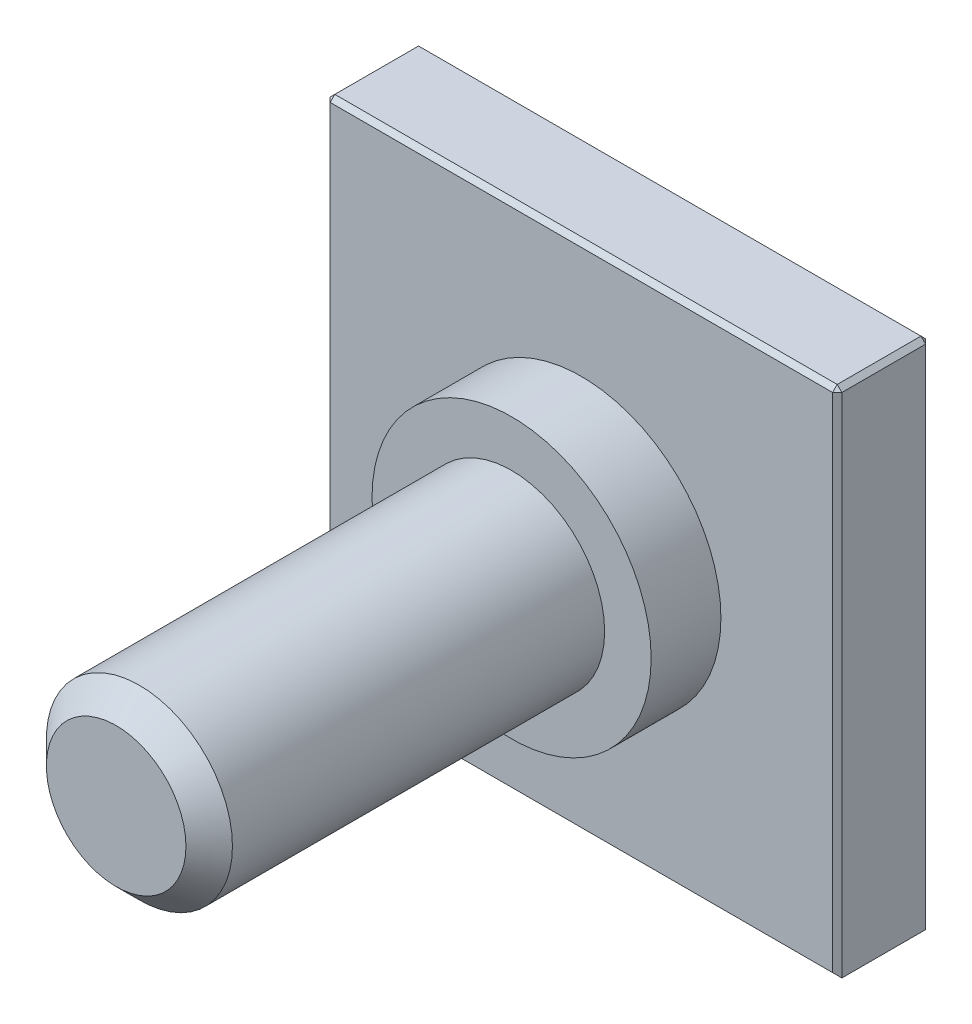
SolidWorks part; units mm, degrees
ref_plane "Front Plane" through (0, 0, 0) normal (0, 0, 1) x (1, 0, 0)
ref_plane "Top Plane" through (0, 0, 0) normal (0, 1, 0) x (1, 0, 0)
ref_plane "Right Plane" through (0, 0, 0) normal (1, 0, 0) x (0, 0, -1)
sketch "Sketch1" plane through (0, 0, 0) normal (0, 0, 1) x (1, 0, 0)
  line L1 (-5.5, -5.5) -> (5.5, -5.5)
  line L2 (-5.5, -5.5) -> (-5.5, 5.5)
  line L3 (-5.5, 5.5) -> (5.5, 5.5)
  line L4 (5.5, -5.5) -> (5.5, 5.5)
  line L5 (-5.5, -5.5) -> (5.5, 5.5) construction
  line L6 (-5.5, 5.5) -> (5.5, -5.5) construction
  point P0 (0, 0)
  dimension "D1" = 11
  dimension "D2" = 11
extrude "Boss-Extrude1" add sketch "Sketch1" along normal blind 2
sketch "Sketch2" plane through (0, 0, 2) normal (0, 0, 1) x (1, 0, 0)
  circle A0 centre (0, 0) radius 2
  dimension "D1" = 4
extrude "Boss-Extrude2" add sketch "Sketch2" along normal blind 10
chamfer "Chamfer1" distance 0.1 angle 45 10 edges at (-5.5, 0, 0) (0, -5.5, 0) (5.5, 0, 0) (-5.5, 0, 2) (0, -5.5, 2) (5.5, 0, 2) (5.5, 5.5, 1) (0, 5.5, 2) (0, 5.5, 0) (-5.5, 5.5, 1)
sketch "Sketch3" plane through (0, 0, 2) normal (0, 0, 1) x (1, 0, 0)
  circle A0 centre (0, 0) radius 3
  dimension "D1" = 6
extrude "Boss-Extrude3" add sketch "Sketch3" along normal blind 1.5
chamfer "Chamfer2" distance 0.5 angle 45 1 edges at (2, 0, 12)
